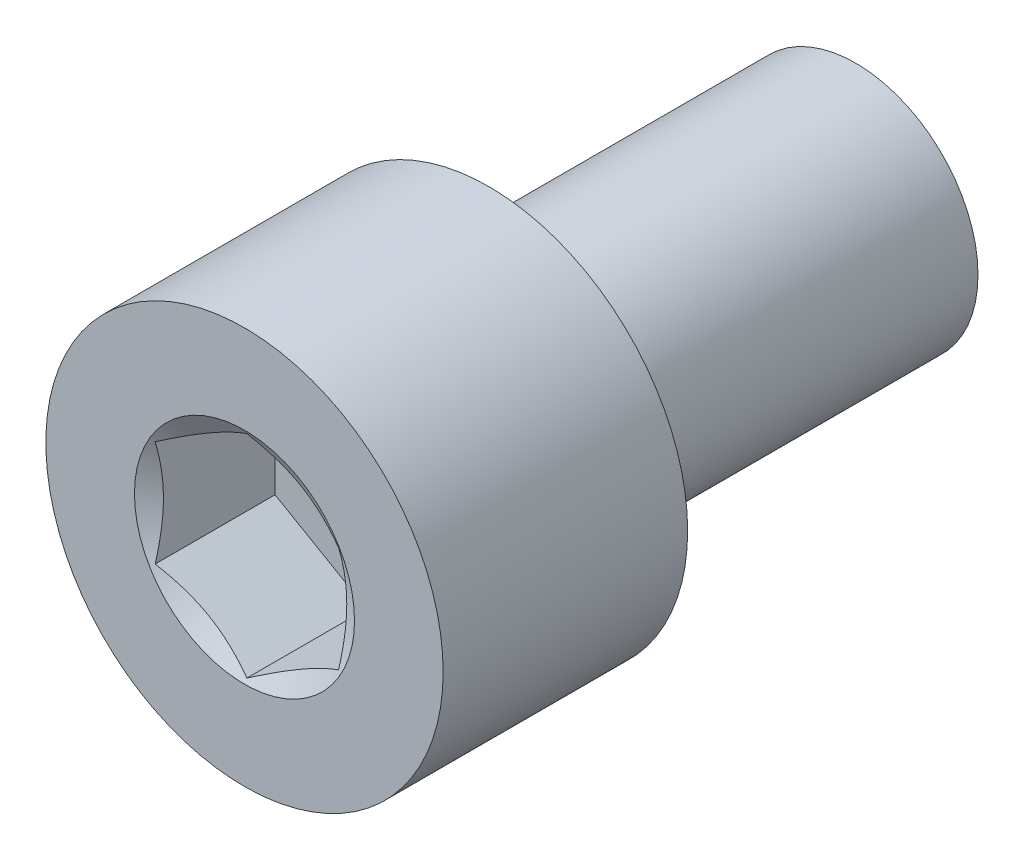
SolidWorks part; units mm, degrees
ref_plane "Плоскость1" through (0, 0, 0) normal (0, 0, 1) x (1, 0, 0)
ref_plane "Плоскость2" through (0, 0, 0) normal (0, 1, 0) x (1, 0, 0)
ref_plane "Плоскость3" through (0, 0, 0) normal (1, 0, 0) x (0, 0, -1)
sketch "Ske1" plane through (0, 0, 0) normal (0, 0, 1) x (1, 0, 0)
  circle A0 centre (0, 0) radius 6.5
  dimension "Head_Dia" = 13
extrude "Base1" add sketch "Ske1" along normal blind 8
sketch "BodySke" plane through (0, 0, 0) normal (1, 0, 0) x (0, 0, -1)
  line L0 (-1.3858, 0) -> (12, 0) construction
  line L1 (0, -6.5) -> (0, 6.5) construction
  line L3 (-8, 0) -> (0, 0) construction
  line L4 (12, 4) -> (-8, 4)
  line L7 (-8, 6.5) -> (-8, -6.5) construction
  line L8 (-8, 4) -> (-8, 0)
  line L9 (-8, 0) -> (12, 0)
  line L10 (12, 0) -> (12, 4)
  line L11 (-8, 0) -> (9.169, 0) construction
  line L12 (1.25, 0) -> (1.25, 5.6548) construction
  line L13 (0, 0) -> (0, 5.6548) construction
  dimension "Diameter" = 8
  dimension "Advance" = 1.25
  dimension "Thread_nom" = 12
  dimension "Length" = 12
revolve "BaseBody" add sketch "BodySke" angle 360 about L0
cosmetic thread "ThreadCosmetic" parameters "Thread_length"=9.5, "Thread_minor"=6.619
sketch "Ske8" plane through (0, 0, 8) normal (0, 0, 1) x (1, 0, 0)
  line L1 (0, 3.4641) -> (-3, 1.7321)
  line L2 (-3, 1.7321) -> (-3, -1.7321)
  line L3 (-3, -1.7321) -> (0, -3.4641)
  line L4 (0, -3.4641) -> (3, -1.7321)
  line L5 (3, -1.7321) -> (3, 1.7321)
  line L6 (3, 1.7321) -> (0, 3.4641)
  circle A0 centre (0, 0) radius 3 construction
  dimension "Width_Flats" = 6
extrude "Hex" cut sketch "Ske8" against normal blind 4
sketch "Ske9" plane through (0, 0, 8) normal (0, 0, 1) x (1, 0, 0)
  circle A1 centre (0, 0) radius 3.6
  dimension "Head_Fillet" = 7.2
extrude "Chamfer" cut sketch "Ske9" against normal through all draft 60
equation "\"Thread_length@ThreadCosmetic\" = ((sgn( (\"Length@BodySke\" - \"Advance@BodySke\" * 2.0 ) - \"Thread_nom@BodySke\" )-1)*( (\"Length@BodySke\" - \"Advance@BodySke\"  * 2.0) - \"Thread_nom@BodySke\" ))/-2+ \"Thread_nom@BodySke\""
